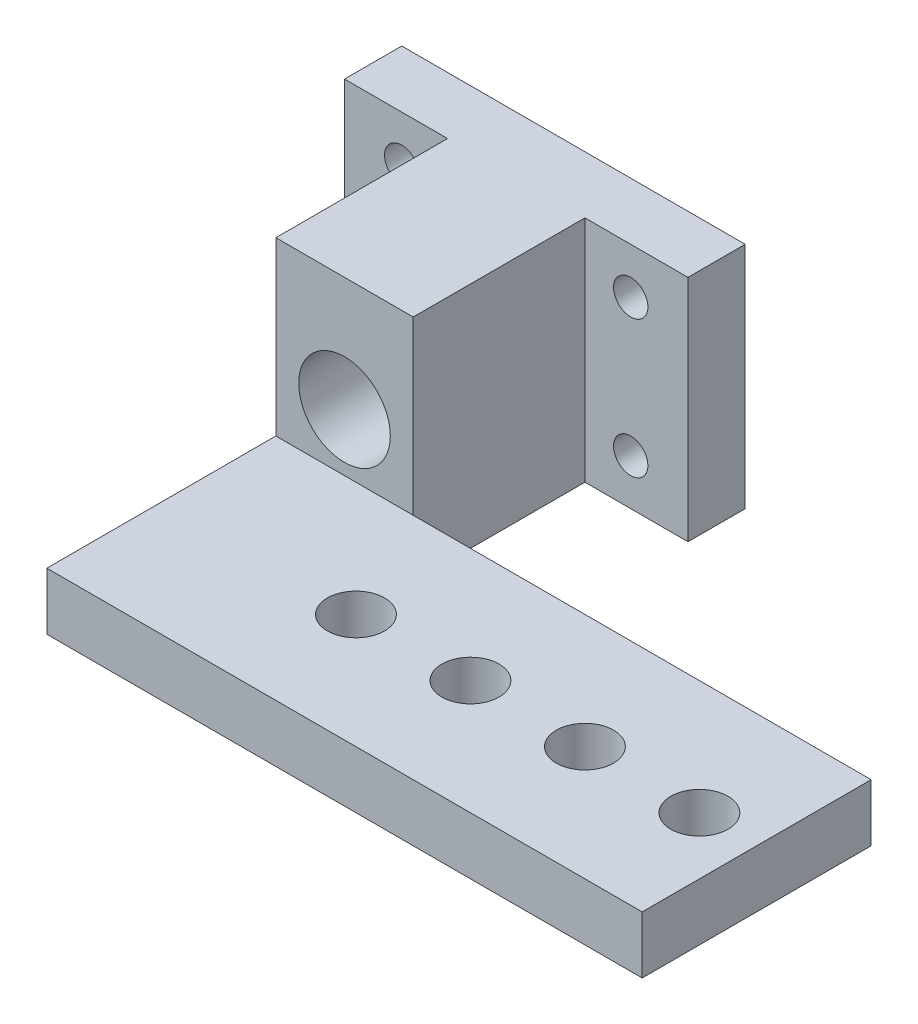
SolidWorks part; units mm, degrees
ref_plane "前视基准面" through (0, 0, 0) normal (0, 0, 1) x (1, 0, 0)
ref_plane "上视基准面" through (0, 0, 0) normal (0, 1, 0) x (1, 0, 0)
ref_plane "右视基准面" through (0, 0, 0) normal (1, 0, 0) x (0, 0, -1)
sketch "草图1" plane through (0, 0, 0) normal (0, 0, 1) x (1, 0, 0)
  line L0 (15, 0) -> (15, -20) construction
  line L1 (0, 0) -> (30, 0)
  line L2 (0, 0) -> (0, -20)
  line L3 (0, -20) -> (30, -20)
  line L4 (30, 0) -> (30, -20)
  line L5 (0, -10) -> (30, -10) construction
  circle A0 centre (5, -4) radius 1.5
  circle A1 centre (25, -4) radius 1.5
  circle A2 centre (25, -16) radius 1.5
  circle A3 centre (5, -16) radius 1.5
  circle A4 centre (15, -10) radius 4
  dimension "D3" = 3
  dimension "D6" = 8
  dimension "D1" = 30
  dimension "D2" = 20
  dimension "D4" = 20
  dimension "D5" = 12
extrude "凸台-拉伸1" add sketch "草图1" along normal blind 20
sketch "草图2" plane through (0, 0, 20) normal (0, 0, 1) x (1, 0, 0)
  line L0 (0, -20) -> (30, -20) construction
  line L1 (0, 0) -> (9, 0)
  line L2 (0, 0) -> (0, -20)
  line L3 (0, -20) -> (9, -20)
  line L4 (9, 0) -> (9, -20)
  line L6 (30, 0) -> (21, 0)
  line L7 (30, 0) -> (30, -20)
  line L8 (30, -20) -> (21, -20)
  line L9 (21, 0) -> (21, -20)
  dimension "D1" = 9
  dimension "D2" = 9
extrude "切除-拉伸1" cut sketch "草图2" against normal blind 15
sketch "草图3" plane through (0, 0, 20) normal (0, 0, 1) x (1, 0, 0)
  line L0 (9, -20) -> (9, 0) construction
  line L1 (9, -15) -> (21, -15)
  line L2 (9, -15) -> (9, -20)
  line L3 (9, -20) -> (21, -20)
  line L4 (21, -15) -> (21, -20)
  dimension "D1" = 5
extrude "凸台-拉伸2" add sketch "草图3" along normal blind 20
sketch "草图4" plane through (21, 0, 0) normal (1, 0, 0) x (0, 0, -1)
  line L0 (-5, -20) -> (-40, -20) construction
  line L1 (-40, -15) -> (-20, -15)
  line L2 (-40, -15) -> (-40, -20)
  line L3 (-40, -20) -> (-20, -20)
  line L4 (-20, -15) -> (-20, -20)
  dimension "D1" = 20
extrude "凸台-拉伸3" add sketch "草图4" along normal blind 40
sketch "草图5" plane through (0, -15, 0) normal (0, 1, 0) x (1, 0, 0)
  line L0 (21, -20) -> (21, -40) construction
  line L1 (61, -40) -> (9, -40) construction
  circle A0 centre (26, -30) radius 2.5
  circle A1 centre (36, -30) radius 2.5
  circle A2 centre (46, -30) radius 2.5
  circle A3 centre (56, -30) radius 2.5
  dimension "D2" = 5
  dimension "D1" = 5
  dimension "D3" = 4
extrude "切除-拉伸2" cut sketch "草图5" against normal blind 20
